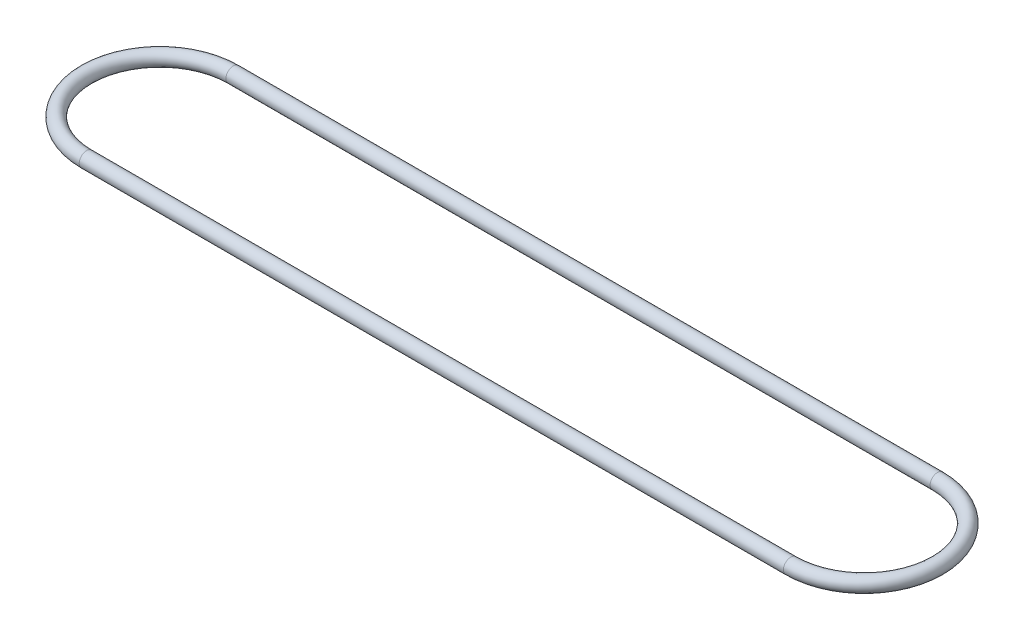
SolidWorks part; units mm, degrees
ref_plane "Front" through (0, 0, 0) normal (0, 0, 1) x (1, 0, 0)
ref_plane "Top" through (0, 0, 0) normal (0, 1, 0) x (1, 0, 0)
ref_plane "Right" through (0, 0, 0) normal (1, 0, 0) x (0, 0, -1)
sketch "Sketch1" plane through (0, 0, 0) normal (0, 1, 0) x (1, 0, 0)
  line L1 (0, 0) -> (304.8, 0)
  line L3 (0, 63.5) -> (304.8, 63.5)
  arc A0 (0, 63.5) -> (0, 0) centre (0, 31.75) ccw
  arc A1 (304.8, 0) -> (304.8, 63.5) centre (304.8, 31.75) ccw
  dimension "D1" = 63.5
  dimension "D2" = 304.8
sketch "Sketch2" plane through (0, 0, 0) normal (1, 0, 0) x (0, 0, -1)
  circle A0 centre (0, 0) radius 3.175
  dimension "D1" = 6.35
sweep "Sweep1" add profiles "Sketch2" path "Sketch1"
